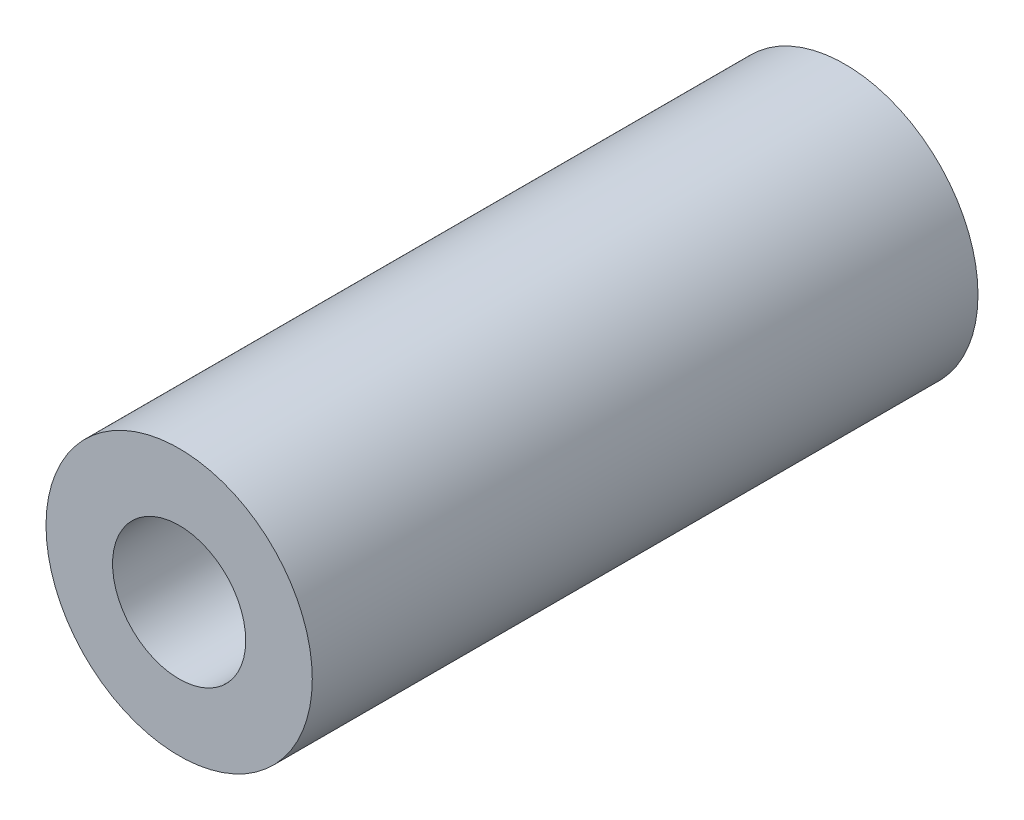
SolidWorks part; units mm, degrees
ref_plane "前视基准面" through (0, 0, 0) normal (0, 0, 1) x (1, 0, 0)
ref_plane "上视基准面" through (0, 0, 0) normal (0, 1, 0) x (1, 0, 0)
ref_plane "右视基准面" through (0, 0, 0) normal (1, 0, 0) x (0, 0, -1)
sketch "草图1" plane through (0, 0, 0) normal (0, 0, 1) x (1, 0, 0)
  circle A0 centre (0, 0) radius 8
  point P0 (0, 0)
extrude "凸台-拉伸1" add sketch "草图1" along normal blind 20
sketch "草图2" plane through (0, 0, 20) normal (0, 0, 1) x (1, 0, 0)
  circle A0 centre (0, 0) radius 4
extrude "切除-拉伸1" cut sketch "草图2" against normal blind 13
mirror "镜向1" about plane through (0, 0, 0) normal (0, 0, 1) of bodies 107
